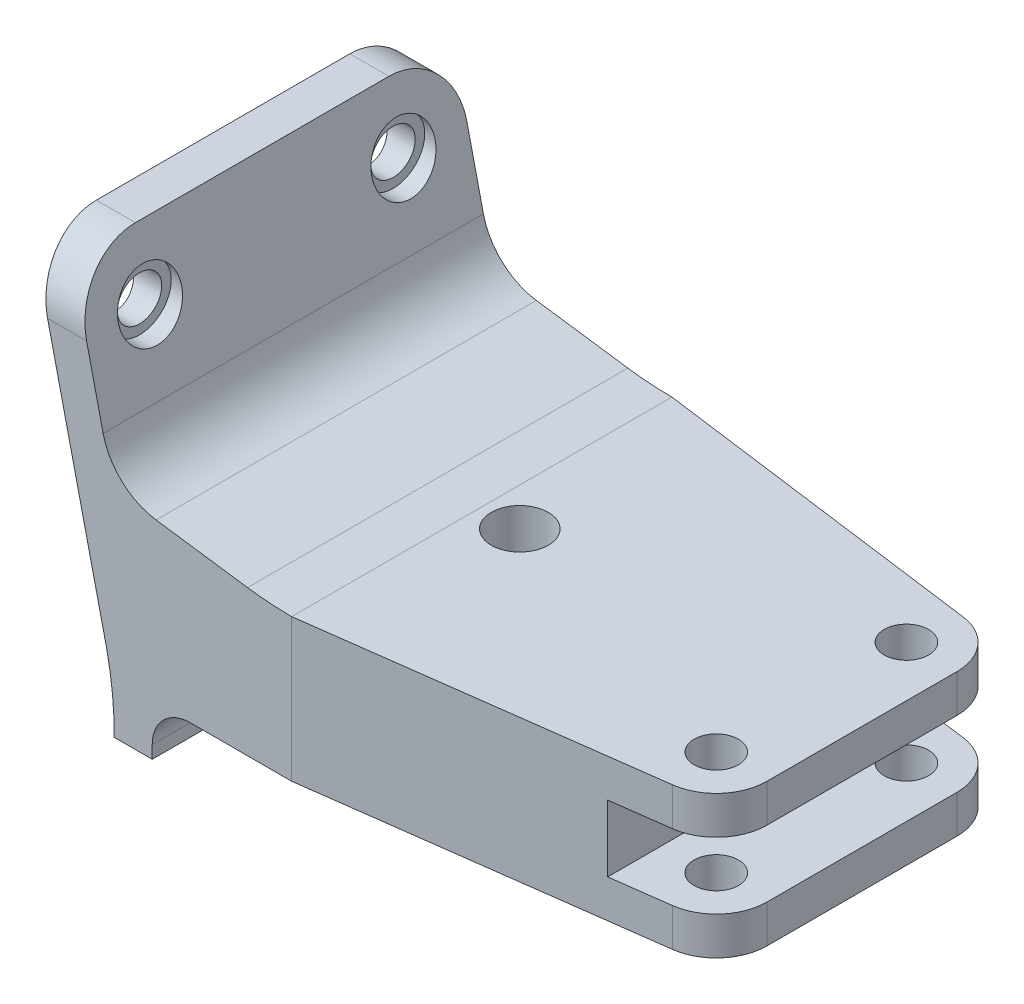
SolidWorks part; units mm, degrees
ref_plane "Front Plane" through (0, 0, 0) normal (0, 0, 1) x (1, 0, 0)
ref_plane "Top Plane" through (0, 0, 0) normal (0, 1, 0) x (1, 0, 0)
ref_plane "Right Plane" through (0, 0, 0) normal (1, 0, 0) x (0, 0, -1)
sketch "Sketch1" plane through (0, 0, 0) normal (0, 0, 1) x (1, 0, 0)
  line L1 (25.4164, 5.478) -> (19.3601, 31.75)
  line L2 (29.3045, 16.2569) -> (36.5224, 15.2431)
  line L3 (40, 15) -> (70, 15)
  line L4 (32, 3.75) -> (70, 3.75)
  line L5 (70, 3.75) -> (70, 6.75)
  line L6 (70, 6.75) -> (62, 6.75)
  line L7 (70, 15) -> (70, 12)
  line L8 (70, 12) -> (62, 12)
  line L9 (62, 12) -> (62, 6.75)
  line L14 (25.1278, 20.0852) -> (22.4388, 31.75)
  line L15 (22.4388, 31.75) -> (19.3601, 31.75)
  line L16 (-2.9992, 0) -> (46.9899, 0) construction
  line L18 (0, -2.9361) -> (0, 15.132) construction
  line L19 (29, 0.75) -> (29, -0.25)
  line L20 (25.9988, -0.25) -> (29, -0.25)
  arc A1 (25.9988, -0.25) -> (25.4164, 5.478) centre (0, 0) ccw
  arc A2 (29.3045, 16.2569) -> (25.1278, 20.0852) centre (30, 21.2083) cw
  arc A3 (36.5224, 15.2431) -> (40, 15) centre (40, 40) ccw
  arc A4 (32, 3.75) -> (29, 0.75) centre (32, 0.75) ccw
  point P1 (32.9135, 15.75)
  point P6 (30, 20.4099)
  dimension "D4" = 5
  dimension "D8" = 25
  dimension "D13" = 3
  dimension "D14" = 4
  dimension "D16" = 26
  dimension "D1" = 5.25
  dimension "D2" = 3
  dimension "D3" = 3
  dimension "D5" = 3.75
  dimension "D6" = 62
  dimension "D7" = 8
  dimension "D9" = 28
  dimension "D10" = 3
  dimension "D11" = 30
  dimension "D12" = 40
  dimension "D15" = 38
  dimension "D17" = 12
  dimension "D18" = 77.019
extrude "Boss-Extrude1" add sketch "Sketch1" along normal mid plane 30
sketch "Sketch2" plane through (0, 15, 0) normal (0, 1, 0) x (1, 0, 0)
  line L0 (70, 0) -> (40, 0) construction
  line L1 (70, -15) -> (70, 15) construction
  line L2 (40, -15) -> (40, 15) construction
  line L3 (70, 7.5) -> (70, 15)
  line L4 (70, 15) -> (40, 15)
  line L5 (40, 15) -> (66.5284, 11.465)
  line L6 (40, -15) -> (66.5284, -11.465)
  line L7 (70, -15) -> (40, -15)
  line L8 (70, -7.5) -> (70, -15)
  circle A0 centre (66, 7.5) radius 1.75
  arc A1 (70, -7.5) -> (66.5284, -11.465) centre (66, -7.5) cw
  arc A2 (70, 7.5) -> (66.5284, 11.465) centre (66, 7.5) ccw
  circle A3 centre (43, 0) radius 2.25
  circle A4 centre (66, -7.5) radius 1.75
  dimension "D3" = 3.5
  dimension "D8" = 4.5
  dimension "D2" = 7.5
  dimension "D5" = 4
  dimension "D7" = 27
extrude "Cut-Extrude1" cut sketch "Sketch2" against normal through all
sketch "Sketch6" plane through (70, 0, 0) normal (1, 0, 0) x (0, 0, -1)
  line L0 (0, 16.2569) -> (0, 37.8385) construction
  line L1 (-15, 16.2569) -> (15, 16.2569) construction
  line L3 (-15, 31.75) -> (15, 31.75) construction
  line L4 (-15, 20.0852) -> (-15, 31.75) construction
  line L5 (-10, 30.75) -> (10, 30.75)
  line L6 (-15, 31.75) -> (15, 31.75)
  line L7 (-15, 31.75) -> (-15, 25.75)
  line L8 (15, 31.75) -> (15, 25.75)
  circle A0 centre (-10, 25.75) radius 1.75
  arc A1 (-10, 30.75) -> (-15, 25.75) centre (-10, 25.75) ccw
  arc A2 (10, 30.75) -> (15, 25.75) centre (10, 25.75) cw
  circle A3 centre (10, 25.75) radius 1.75
  point P14 (0, 30.75)
  point P21 (0, 31.75)
  dimension "D2" = 3.5
  dimension "D1" = 10
  dimension "D3" = 6
extrude "Cut-Extrude4" cut sketch "Sketch6" against normal through all
ref_plane "Plane1" through (25, 0, 0) normal (1, 0, 0) x (0, 0, -1)
sketch "Sketch8" plane through (25, 0, 0) normal (1, 0, 0) x (0, 0, -1)
  line L0 (0, -0.7256) -> (0, 33.0427) construction
  circle A0 centre (-10, 25.75) radius 2.5
  circle A1 centre (10, 25.75) radius 2.5
  dimension "D1" = 5
extrude "Cut-Extrude5" cut sketch "Sketch8" against normal blind 2
